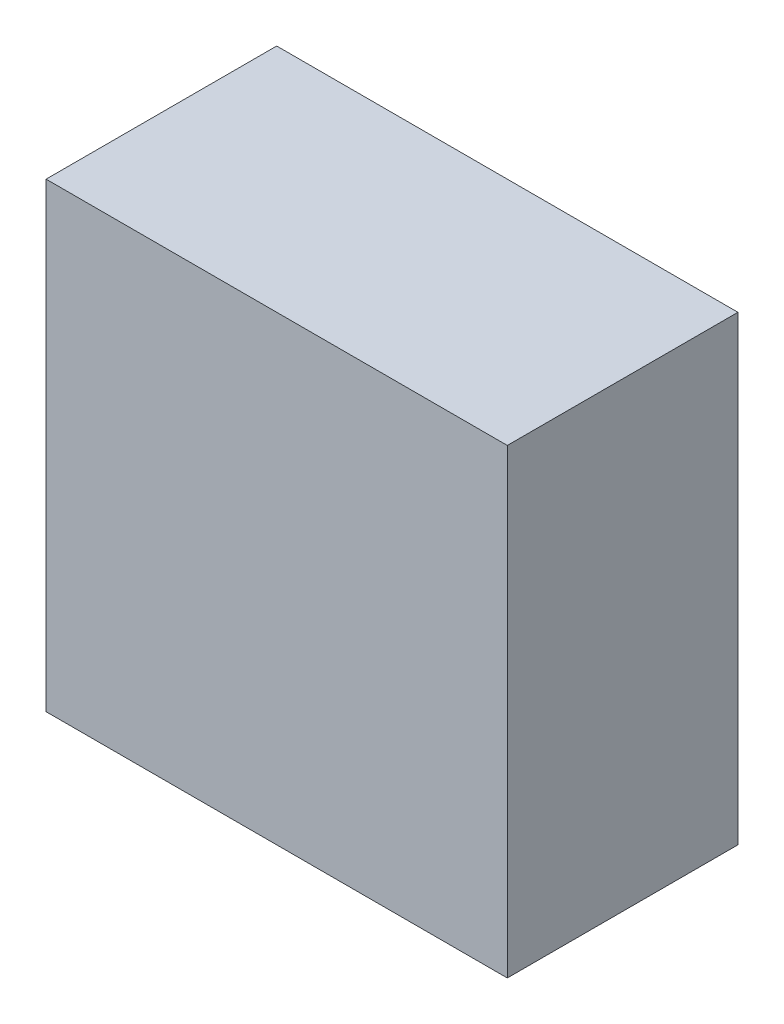
SolidWorks part; units mm, degrees
ref_plane "前视基准面" through (0, 0, 0) normal (0, 0, 1) x (1, 0, 0)
ref_plane "上视基准面" through (0, 0, 0) normal (0, 1, 0) x (1, 0, 0)
ref_plane "右视基准面" through (0, 0, 0) normal (1, 0, 0) x (0, 0, -1)
sketch "草图1" plane through (0, 0, 0) normal (0, 0, 1) x (1, 0, 0)
  line L1 (-20, -20) -> (20, -20)
  line L2 (-20, -20) -> (-20, 20)
  line L3 (-20, 20) -> (20, 20)
  line L4 (20, -20) -> (20, 20)
  line L5 (-20, -20) -> (20, 20) construction
  line L6 (-20, 20) -> (20, -20) construction
  point P1 (0, 0)
  dimension "D1" = 40
  dimension "D2" = 40
extrude "凸台-拉伸1" add sketch "草图1" along normal blind 20
